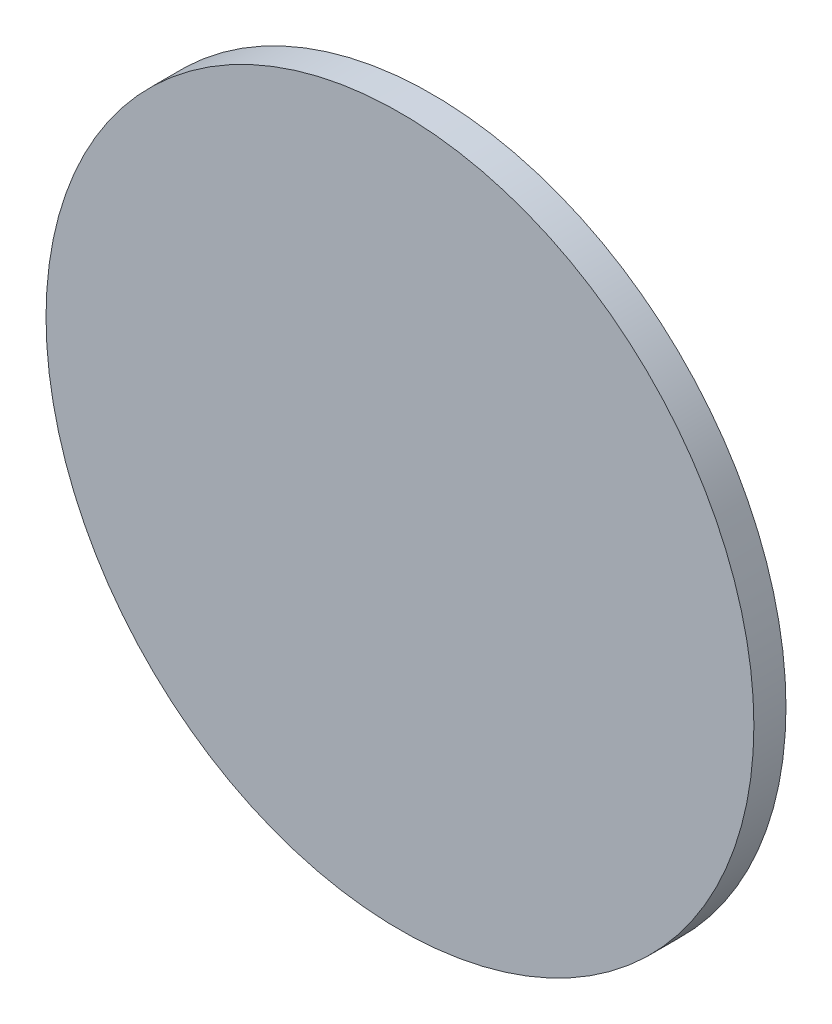
SolidWorks part; units mm, degrees
material "Barium"
ref_plane "Front" through (0, 0, 0) normal (0, 0, 1) x (1, 0, 0)
ref_plane "Top" through (0, 0, 0) normal (0, 1, 0) x (1, 0, 0)
ref_plane "Right" through (0, 0, 0) normal (1, 0, 0) x (0, 0, -1)
sketch "Sketch1" plane through (0, 0, 0) normal (0, 0, 1) x (1, 0, 0)
  circle A2 centre (0, 0) radius 75
extrude "Boss-Extrude1" add sketch "Sketch1" along normal blind 6.8 contours A2
